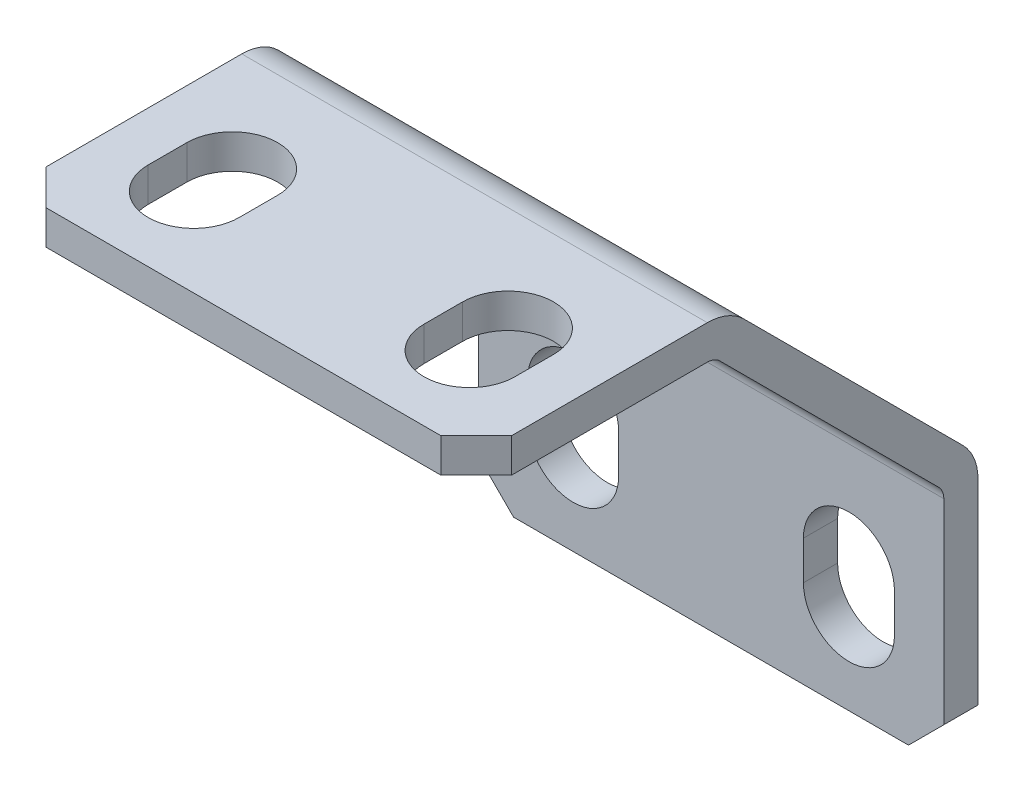
SolidWorks part; units mm, degrees
material "Custom Plastic"
ref_plane "Front Plane" through (0, 0, 0) normal (0, 0, 1) x (1, 0, 0)
ref_plane "Top Plane" through (0, 0, 0) normal (0, 1, 0) x (1, 0, 0)
ref_plane "Right Plane" through (0, 0, 0) normal (1, 0, 0) x (0, 0, -1)
ref_plane "Plane1" through (10.7188, 0, 0) normal (1, 0, 0) x (0, 0, -1)
sketch "Sketch1" plane through (10.7188, 0, 0) normal (1, 0, 0) x (0, 0, -1)
  line L0 (-23.1063, 17.7859) -> (-23.1063, -5.3213)
  line L1 (-23.1063, -5.3213) -> (0, -5.3213)
  line L2 (0, -5.3213) -> (0, 6.3103)
  line L3 (0, 6.3103) -> (-11.4756, 17.7859)
  line L4 (-11.4756, 17.7859) -> (-23.1063, 17.7859)
extrude "Boss-Extrude1" add sketch "Sketch1" against normal blind 21.4376
sketch "Sketch2" plane through (-10.7188, 0, 0) normal (-1, 0, 0) x (0, 0, 1)
  line L0 (23.1063, -5.3213) -> (23.1063, 16.2111)
  line L1 (23.1063, 16.2111) -> (12.1279, 16.2111)
  line L2 (12.1279, 16.2111) -> (1.5748, 5.658)
  line L3 (1.5748, 5.658) -> (1.5748, -5.3213)
  line L4 (1.5748, -5.3213) -> (23.1063, -5.3213)
extrude "Cut-Extrude1" cut sketch "Sketch2" against normal through all
sketch "Sketch3" plane through (0, 16.2111, 0) normal (0, -1, 0) x (1, 0, 0)
  line L0 (-4.2545, 17.272) -> (-4.2545, 19.05)
  line L1 (-8.4455, 19.05) -> (-8.4455, 17.272)
  arc A0 (-4.2545, 19.05) -> (-8.4455, 19.05) centre (-6.35, 19.05) ccw
  arc A1 (-8.4455, 17.272) -> (-4.2545, 17.272) centre (-6.35, 17.272) ccw
extrude "Cut-Extrude2" cut sketch "Sketch3" against normal through all
sketch "Sketch4" plane through (0, 17.7859, 0) normal (0, 1, 0) x (-1, 0, 0)
  line L0 (-8.4455, 19.05) -> (-8.4455, 17.272)
  line L1 (-4.2545, 17.272) -> (-4.2545, 19.05)
  arc A0 (-8.4455, 17.272) -> (-4.2545, 17.272) centre (-6.35, 17.272) ccw
  arc A1 (-4.2545, 19.05) -> (-8.4455, 19.05) centre (-6.35, 19.05) ccw
extrude "Cut-Extrude3" cut sketch "Sketch4" against normal through all
sketch "Sketch5" plane through (0, 0, 1.5748) normal (0, 0, 1) x (1, 0, 0)
  line L0 (4.2545, 0.5139) -> (4.2545, -1.2641)
  line L1 (8.4455, -1.2641) -> (8.4455, 0.5139)
  arc A0 (4.2545, -1.2641) -> (8.4455, -1.2641) centre (6.35, -1.2641) ccw
  arc A1 (8.4455, 0.5139) -> (4.2545, 0.5139) centre (6.35, 0.5139) ccw
extrude "Cut-Extrude4" cut sketch "Sketch5" against normal through all
sketch "Sketch6" plane through (0, 0, 0) normal (0, 0, -1) x (-1, 0, 0)
  line L0 (8.4455, -1.2641) -> (8.4455, 0.5139)
  line L1 (4.2545, 0.5139) -> (4.2545, -1.2641)
  arc A0 (8.4455, 0.5139) -> (4.2545, 0.5139) centre (6.35, 0.5139) ccw
  arc A1 (4.2545, -1.2641) -> (8.4455, -1.2641) centre (6.35, -1.2641) ccw
extrude "Cut-Extrude5" cut sketch "Sketch6" against normal through all
chamfer "Chamfer1" distance 1.6256 angle 45 4 edges at (10.7188, 16.9985, 23.1063) (10.7188, -5.3213, 0.7874) (-10.7188, 16.9985, 23.1063) (-10.7188, -5.3213, 0.7874)
fillet "Fillet1" radius 0.8128 2 edges at (0, 16.2111, 12.1279) (0, 5.658, 1.5748)
fillet "Fillet2" radius 2.3876 2 edges at (0, 6.3103, 0) (0, 17.7859, 11.4756)
